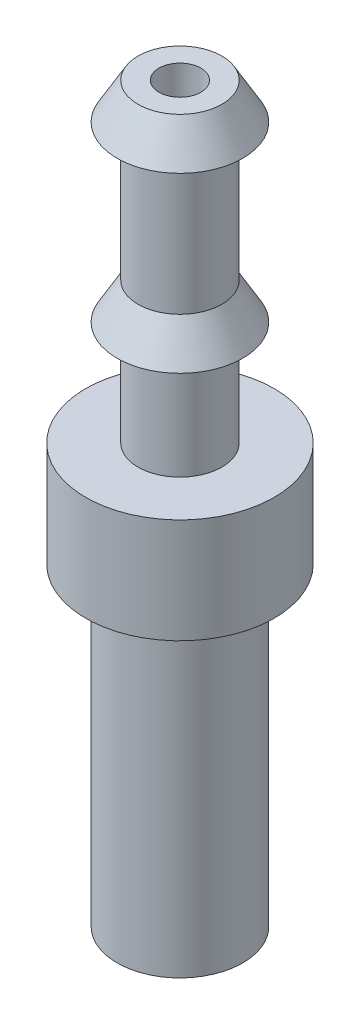
SolidWorks part; units mm, degrees
ref_plane "Спереди" through (0, 0, 0) normal (0, 0, 1) x (1, 0, 0)
ref_plane "Сверху" through (0, 0, 0) normal (0, 1, 0) x (1, 0, 0)
ref_plane "Справа" through (0, 0, 0) normal (1, 0, 0) x (0, 0, -1)
sketch "Эскиз1" plane through (0, 0, 0) normal (0, 0, 1) x (1, 0, 0)
  line L0 (0, 0) -> (0, -15) construction
  line L1 (-1, -15) -> (-3, -15)
  line L2 (-3, -15) -> (-3, 0)
  line L3 (-3, 0) -> (-4.5, 0)
  line L4 (-4.5, 0) -> (-4.5, 5)
  line L5 (-4.5, 5) -> (-2, 5)
  line L6 (-2, 5) -> (-2, 10)
  line L7 (-2, 10) -> (-3, 10)
  line L8 (-3, 10) -> (-2, 11.7321)
  line L9 (-2, 11.7321) -> (-2, 18.2679)
  line L10 (-2, 18.2679) -> (-3, 18.2679)
  line L11 (-3, 18.2679) -> (-2, 20)
  line L13 (-2, 20) -> (-1, 20)
  line L14 (-1, 20) -> (-1, -15)
  line L15 (0, 0) -> (0, 20) construction
  line L16 (-1, 20) -> (0, 20) construction
  line L17 (0, -15) -> (-1, -15) construction
  line L18 (-3, 18.2679) -> (-3, 10) construction
  dimension "D1" = 2
  dimension "D2" = 6
  dimension "D3" = 5
  dimension "D4" = 4
  dimension "D5" = 60
  dimension "D6" = 60
  dimension "D7" = 15
  dimension "D8" = 15
  dimension "D9" = 9
  dimension "D10" = 10
  dimension "D11" = 6
  dimension "D12" = 1
  dimension "D13" = 4
revolve "Повернуть1" add sketch "Эскиз1" angle 360 about L15
